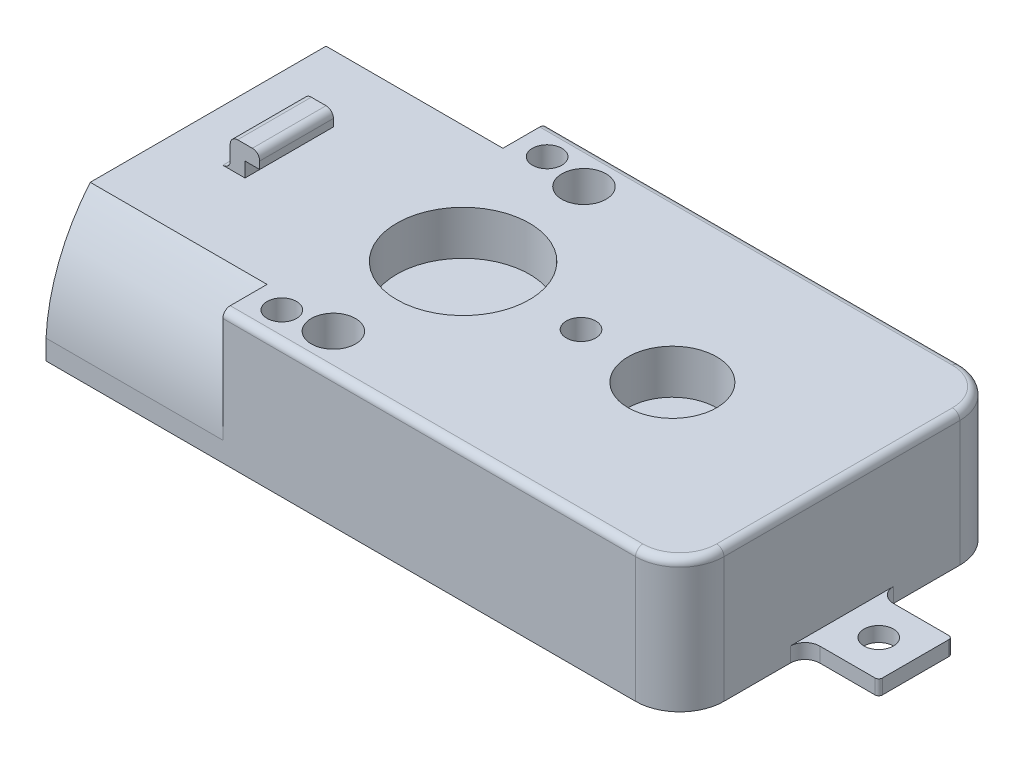
SolidWorks part; units mm, degrees
ref_plane "Front Plane" through (0, 0, 0) normal (0, 0, 1) x (1, 0, 0)
ref_plane "Top Plane" through (0, 0, 0) normal (0, 1, 0) x (1, 0, 0)
ref_plane "Right Plane" through (0, 0, 0) normal (1, 0, 0) x (0, 0, -1)
sketch "Sketch2" plane through (0, 0, 0) normal (0, 1, 0) x (1, 0, 0)
  line L0 (31, 11) -> (0, 11) construction
  line L1 (0, 0) -> (31, 0)
  line L2 (0, 0) -> (0, 22)
  line L3 (0, 22) -> (31, 22)
  line L4 (31, 0) -> (31, 22)
  line L7 (31, 8.5) -> (31, 13.5)
  dimension "48" = 31
  dimension "22" = 22
extrude "Boss-Extrude2" add sketch "Sketch2" along normal blind 9 contours L0 L7 L4 L3 L2 | L4 L0 L2 L1
sketch "Sketch4" plane through (31, 0, 0) normal (1, 0, 0) x (0, 0, -1)
  line L0 (0, 0) -> (22, 0) construction
  line L1 (8.5, 0) -> (13.5, 0)
  line L2 (8.5, 0) -> (8.5, 1)
  line L3 (8.5, 1) -> (13.5, 1)
  line L4 (13.5, 0) -> (13.5, 1)
  point P6 (11, 1)
  dimension "D1" = 1
  dimension "D2" = 5
  dimension "D3" = 11
extrude "Boss-Extrude3" add sketch "Sketch4" along normal blind 5
sketch "Sketch5" plane through (0, 1, 0) normal (0, 1, 0) x (1, 0, 0)
  circle A0 centre (33.5, 11) radius 1
  dimension "D1" = 2
  dimension "D2" = 2.5
  dimension "D3" = 2.5
extrude "Cut-Extrude1" cut sketch "Sketch5" against normal blind 5
fillet "Fillet1" radius 1 1 edges
fillet "Fillet2" radius 1 1 edges
fillet "Fillet3" radius 3 1 edges at (31, 4.5, 0)
fillet "Fillet4" radius 3 1 edges at (31, 4.5, -22)
sketch "Sketch6" plane through (0, 0, 0) normal (-1, 0, 0) x (0, 0, 1)
  line L0 (-11, 0) -> (-11, 9) construction
  line L1 (0, 0) -> (-22, 0) construction
  line L2 (0, 9) -> (-22, 9) construction
  line L3 (-22, 0) -> (0, 0)
  line L5 (-22, 0) -> (-22.0206, -0.0102)
  line L6 (0, 1.3449) -> (0, 0)
  line L7 (-19, 9) -> (-3, 9)
  line L8 (0, 0) -> (-22, 0)
  arc A0 (0, 0) -> (-3, 9) centre (-12.9826, 0.6725) ccw
  arc A1 (-22, 0) -> (-19, 9) centre (-9.0174, 0.6725) cw
  point P9 (0, 0)
  line M1 (-22, 0) -> (0, 0)
  line M2 (0, 0) -> (0, 9)
  line M3 (0, 9) -> (-22, 9)
  line M4 (-22, 9) -> (-22, 0)
  dimension "D1" = 13
  dimension "D2" = 3
sketch "Sketch7" plane through (0, 0, 0) normal (-1, 0, 0) x (0, 0, 1)
extrude "Boss-Extrude4" add sketch "Sketch6" along normal blind 12 contours L0 L7 A1 M1 M4 | L0 L8 A0 M2 M3
fillet "Fillet5" radius 0.5 5 edges at (14, 9, -22) (30.1213, 9, -21.1213) (31, 9, -11) (30.1213, 9, -0.8787) (14, 9, 0)
fillet "Fillet6" radius 0.25 2 edges at (36, 0.5, -13.5) (36, 0.5, -8.5)
sketch "Sketch8" plane through (0, 9, 0) normal (0, 1, 0) x (1, 0, 0)
  line L0 (30.5, 3) -> (30.5, 19) construction
  circle A0 centre (19.5, 11) radius 3
  point P2 (30.5, 11)
  dimension "D1" = 6
  dimension "D2" = 11
extrude "Cut-Extrude3" cut sketch "Sketch8" against normal blind 3
sketch "Sketch9" plane through (0, 6, 0) normal (0, 1, 0) x (1, 0, 0)
  circle A0 centre (19.5, 11) radius 0.75
  dimension "1,5" = 1.5
extrude "Cut-Extrude4" cut sketch "Sketch9" against normal blind 3
sketch "Sketch10" plane through (0, 9, 0) normal (0, 1, 0) x (1, 0, 0)
  line L0 (-12, 11) -> (30.5, 11) construction
  line L1 (-12, 3) -> (-12, 19) construction
  line L2 (30.5, 3) -> (30.5, 19) construction
  line L4 (28, 0) -> (0, 0) construction
  circle A0 centre (5, 19.5) radius 1.5
  circle A1 centre (5, 2.5) radius 1.5
  dimension "D1" = 3
  dimension "2,5" = 2.5
  dimension "5" = 5
extrude "Cut-Extrude7" cut sketch "Sketch10" against normal through all
sketch "Sketch12" plane through (0, 9, 0) normal (0, 1, 0) x (1, 0, 0)
  line L0 (28, 0) -> (0, 0) construction
  circle A0 centre (2, 2) radius 1
  circle A1 centre (2, 20) radius 1
  dimension "D1" = 2
  dimension "D2" = 2
  dimension "D3" = 2
  dimension "D4" = 2
  dimension "D5" = 2
  dimension "D6" = 2
extrude "Cut-Extrude8" cut sketch "Sketch12" against normal blind 5
sketch "Sketch13" plane through (0, 9, 0) normal (0, 1, 0) x (1, 0, 0)
  line L0 (-12, 11) -> (36, 11) construction
  line L1 (-8, 13.5) -> (-7, 13.5)
  line L2 (-8, 13.5) -> (-8, 8.5)
  line L3 (-8, 8.5) -> (-7, 8.5)
  line L4 (-7, 13.5) -> (-7, 8.5)
  line L5 (-12, 3) -> (-12, 19) construction
  line L6 (36, 13.25) -> (36, 8.75) construction
  dimension "D1" = 4
  dimension "D2" = 1
  dimension "D3" = 5
  dimension "D4" = 2.5
extrude "Boss-Extrude5" add sketch "Sketch13" along normal blind 2
sketch "Sketch14" plane through (-7, 0, 0) normal (1, 0, 0) x (0, 0, -1)
  line L0 (13.5, 11) -> (13.5, 9) construction
  line L1 (8.5, 11) -> (13.5, 11)
  line L2 (8.5, 11) -> (8.5, 10)
  line L3 (8.5, 10) -> (13.5, 10)
  line L4 (13.5, 11) -> (13.5, 10)
extrude "Boss-Extrude6" add sketch "Sketch14" along normal blind 1
fillet "Fillet7" radius 0.5 1 edges at (-8, 11, -11)
fillet "Fillet8" radius 0.5 1 edges at (-8, 9, -11)
fillet "Fillet9" radius 0.5 1 edges at (-6, 11, -11)
sketch "Sketch16" plane through (-12, 0, 0) normal (-1, 0, 0) x (0, 0, 1)
  line L0 (-18.2321, 8.3594) -> (-3.7679, 8.3594)
  line L1 (-21.0013, 1.2932) -> (-21, 0)
  line L2 (-0.9987, 1.2932) -> (-0.9987, 0)
  line L3 (-21, 0) -> (-0.9987, 0)
  arc A2 (-18.2321, 8.3594) -> (-21.0013, 1.2932) centre (-9.0174, 0.6725) ccw
  arc A3 (-18.2321, 8.3594) -> (-21.0013, 1.2932) centre (-9.0174, 0.6725) ccw
  arc A5 (-0.9987, 1.2932) -> (-3.7679, 8.3594) centre (-12.9826, 0.6725) ccw
  arc A6 (-0.9987, 1.2932) -> (-3.7679, 8.3594) centre (-12.9826, 0.6725) ccw
  dimension "D1" = 1
  dimension "D2" = 1
extrude "Cut-Extrude9" cut sketch "Sketch16" against normal blind 10
sketch "Sketch17" plane through (0, 9, 0) normal (0, 1, 0) x (1, 0, 0)
  line L0 (-12, 11) -> (5.3, 11) construction
  line L1 (-12, 3) -> (-12, 19) construction
  line L2 (5.3, 11) -> (13.3, 11) construction
  circle A0 centre (5.3, 11) radius 4.5
  circle A1 centre (13.3, 11) radius 1
  dimension "D2" = 9
  dimension "D4" = 2
  dimension "D1" = 17.3
  dimension "D3" = 8
extrude "Cut-Extrude10" cut sketch "Sketch17" against normal blind 3
